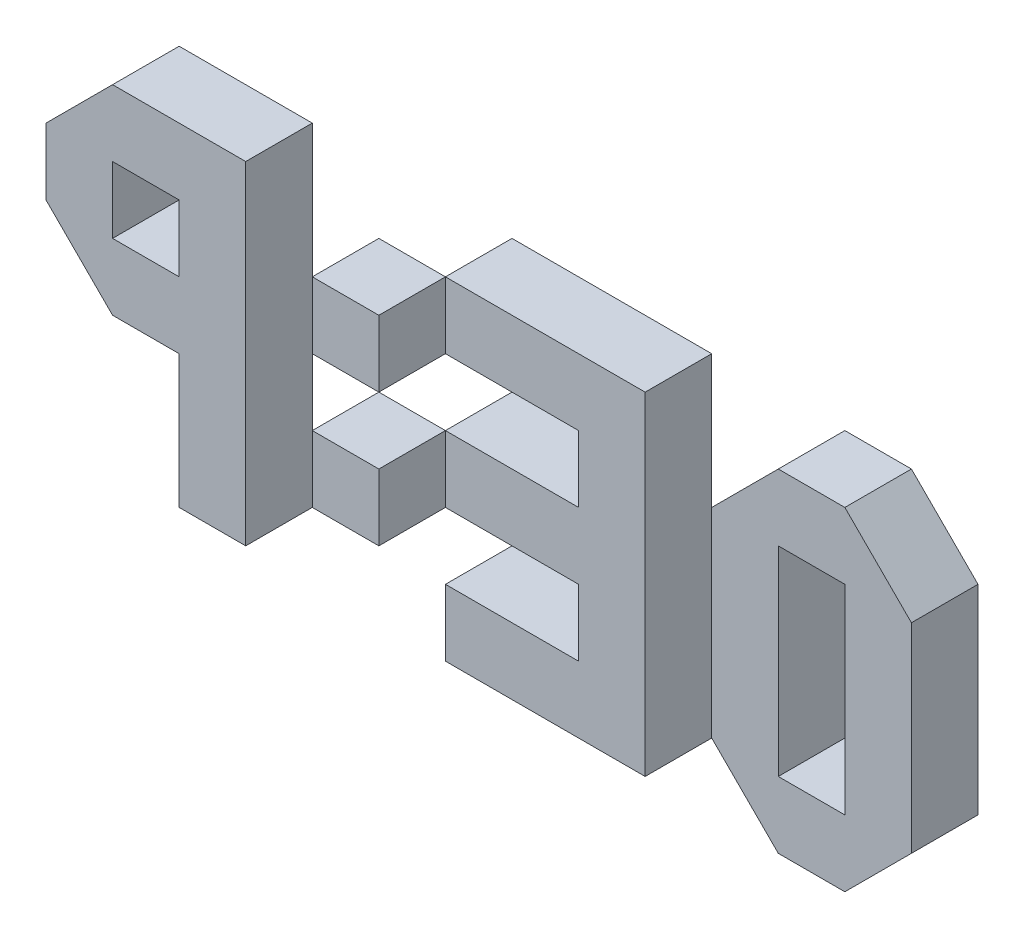
SolidWorks part; units mm, degrees
ref_plane "Front" through (0, 0, 0) normal (0, 0, 1) x (1, 0, 0)
ref_plane "Top" through (0, 0, 0) normal (0, 1, 0) x (1, 0, 0)
ref_plane "Right" through (0, 0, 0) normal (1, 0, 0) x (0, 0, -1)
sketch "Sketch1" plane through (0, 0, 0) normal (0, 0, 1) x (1, 0, 0)
  line L0 (30, 45) -> (30, 60)
  line L1 (30, 0) -> (45, 0)
  line L2 (90, 0) -> (135, 0)
  line L3 (15, 75) -> (45, 75)
  line L4 (195, 15) -> (195, 60)
  line L5 (15, 30) -> (30, 30)
  line L6 (15, 45) -> (30, 45)
  line L7 (15, 60) -> (30, 60)
  line L8 (15, 45) -> (15, 60)
  line L9 (30, 0) -> (30, 30)
  line L10 (45, 0) -> (45, 75)
  line L11 (60, 15) -> (60, 30)
  line L12 (75, 15) -> (75, 30)
  line L13 (90, 0) -> (90, 15)
  line L14 (90, 60) -> (90, 75)
  line L15 (120, 15) -> (120, 30)
  line L16 (135, 0) -> (135, 75)
  line L17 (150, 15) -> (150, 60)
  line L18 (165, 15) -> (165, 60)
  line L19 (180, 15) -> (180, 60)
  line L20 (15, 75) -> (0, 60)
  line L21 (0, 45) -> (15, 30)
  line L22 (180, 75) -> (195, 60)
  line L23 (195, 15) -> (180, 0)
  line L24 (165, 0) -> (150, 15)
  line L25 (165, 75) -> (150, 60)
  line L26 (0, 45) -> (0, 60)
  line L27 (60, 15) -> (75, 15)
  line L28 (0, 0) -> (0, 30) [skipped]
  line L29 (60, 30) -> (75, 30)
  line L30 (60, 45) -> (75, 45)
  line L31 (60, 60) -> (75, 60)
  line L32 (90, 75) -> (135, 75)
  line L33 (90, 60) -> (120, 60)
  line L34 (90, 45) -> (120, 45)
  line L35 (75, 45) -> (75, 60)
  line L36 (60, 45) -> (60, 60)
  line L37 (90, 15) -> (120, 15)
  line L38 (90, 30) -> (120, 30)
  line L39 (15, 15) -> (30, 15) [skipped]
  line L40 (165, 75) -> (180, 75)
  line L41 (165, 60) -> (180, 60)
  line L42 (120, 45) -> (120, 60)
  line L44 (165, 15) -> (180, 15)
  line L45 (165, 0) -> (180, 0)
  line L46 (90, 30) -> (90, 45)
  line L48 (105, 15) -> (105, 30) [skipped]
extrude "Extrude1" add sketch "Sketch1" along normal blind 15
